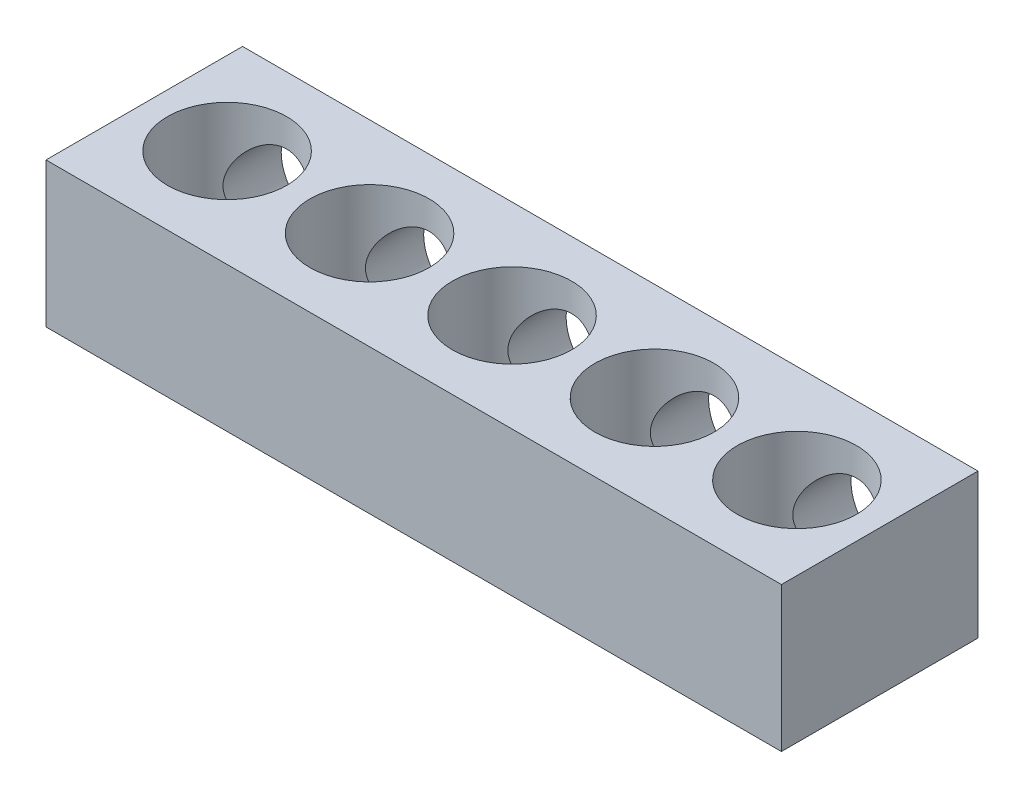
SolidWorks part; units mm, degrees
ref_plane "Front Plane" through (0, 0, 0) normal (0, 0, 1) x (1, 0, 0)
ref_plane "Top Plane" through (0, 0, 0) normal (0, 1, 0) x (1, 0, 0)
ref_plane "Right Plane" through (0, 0, 0) normal (1, 0, 0) x (0, 0, -1)
sketch "Sketch1" plane through (0, 0, 0) normal (0, 1, 0) x (1, 0, 0)
  line L0 (-16.65, 0) -> (16.65, 0) construction
  line L1 (-16.65, 4.45) -> (16.65, 4.45)
  line L2 (-16.65, 4.45) -> (-16.65, -4.45)
  line L3 (-16.65, -4.45) -> (16.65, -4.45)
  line L4 (16.65, 4.45) -> (16.65, -4.45)
  line L5 (-16.65, 4.45) -> (16.65, -4.45) construction
  line L6 (-16.65, -4.45) -> (16.65, 4.45) construction
  line L7 (-12.9, 2.7) -> (-16.65, 2.7) construction
  line L8 (12.9, 2.7) -> (16.65, 2.7) construction
  line L9 (-10.2, 0) -> (-9.15, 0) construction
  line L10 (-16.65, 0) -> (-15.6, 0) construction
  circle A0 centre (-12.9, 0) radius 2.7
  circle A1 centre (-6.45, 0) radius 2.7
  circle A2 centre (0, 0) radius 2.7
  circle A3 centre (6.45, 0) radius 2.7
  circle A4 centre (12.9, 0) radius 2.7
  point P0 (0, 0)
  dimension "D2" = 5.4
  dimension "D1" = 8.9
  dimension "D5" = 6.45
  dimension "D4" = 5
extrude "Boss-Extrude1" add sketch "Sketch1" along normal blind 6.55
sketch "Sketch2" plane through (0, 0, -4.45) normal (0, 0, -1) x (-1, 0, 0)
  line L0 (-10.2, 6.55) -> (-15.6, 6.55) construction
  line L1 (-3.75, 6.55) -> (-9.15, 6.55) construction
  line L2 (2.7, 6.55) -> (-2.7, 6.55) construction
  line L3 (9.15, 6.55) -> (3.75, 6.55) construction
  line L4 (15.6, 6.55) -> (10.2, 6.55) construction
  line L5 (-10.2, 6.55) -> (-15.6, 6.55)
  line L6 (-3.75, 6.55) -> (-9.15, 6.55)
  line L7 (2.7, 6.55) -> (-2.7, 6.55)
  line L8 (9.15, 6.55) -> (3.75, 6.55)
  line L9 (15.6, 6.55) -> (10.2, 6.55)
  line L10 (-12.9, 6.55) -> (-12.9, 0) construction
  line L11 (-16.65, 0) -> (16.65, 0) construction
  line L12 (-6.45, 6.55) -> (-6.45, 0) construction
  line L13 (0, 6.55) -> (0, 0) construction
  line L14 (6.45, 6.55) -> (6.45, 0) construction
  line L15 (12.9, 6.55) -> (12.9, 0) construction
  circle A0 centre (-12.9, 3.275) radius 2
  circle A1 centre (-6.45, 3.275) radius 2
  circle A2 centre (0, 3.275) radius 2
  circle A3 centre (6.45, 3.275) radius 2
  circle A4 centre (12.9, 3.275) radius 2
  dimension "D1" = 4
extrude "Cut-Extrude1" cut sketch "Sketch2" against normal up to next contours A0 | A1 | A2 | A3 | A4
